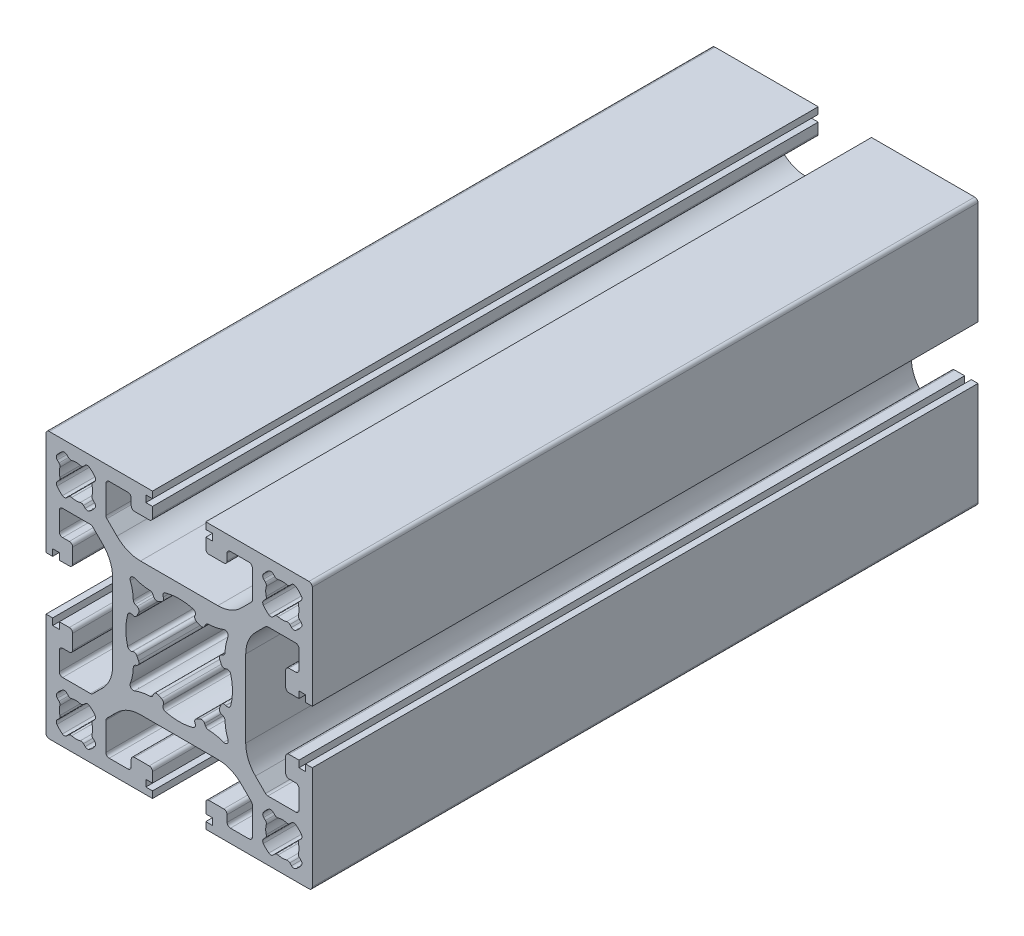
SolidWorks part; units mm, degrees
ref_plane "Front Plane" through (0, 0, 0) normal (0, 0, 1) x (1, 0, 0)
ref_plane "Top Plane" through (0, 0, 0) normal (0, 1, 0) x (1, 0, 0)
ref_plane "Right Plane" through (0, 0, 0) normal (1, 0, 0) x (0, 0, -1)
sketch "Sketch1" plane through (0, 0, 0) normal (0, 0, 1) x (1, 0, 0)
  line L0 (0, -10) -> (0, 10) construction
  line L1 (10, 0) -> (-10, 0) construction
  line L2 (11, 17.5) -> (11, 13.3284)
  line L3 (4, 20) -> (4, 19)
  line L4 (-10.8536, 12.9749) -> (-9.3431, 11.4645)
  line L5 (-12.9749, 10.8536) -> (-11.4645, 9.3431)
  line L6 (19.5, 20) -> (4, 20)
  line L7 (20, 4.5) -> (20, 19.5)
  line L8 (-3.9555, 6.5896) -> (-3.8287, 6.3177)
  line L9 (-2.3966, 7.0325) -> (-2.3786, 6.9939)
  line L10 (-6.7, 16) -> (-4.5, 16)
  line L11 (16.5, 4) -> (18, 4)
  line L12 (16, 6.7) -> (16, 4.5)
  line L13 (13.3284, 11) -> (16, 11)
  line L14 (10, -5.8076) -> (10, 5.8076)
  line L15 (-7.043, 2.3972) -> (-6.995, 2.3748)
  line L16 (-6.599, 3.9553) -> (-6.3199, 3.8254)
  line L17 (-14.1155, 18.2988) -> (-14.37, 18.0442)
  line L18 (18, 4) -> (18, 5)
  line L19 (-12.7012, 16.8845) -> (-12.9558, 16.63)
  line L20 (-10.5, 18) -> (-7.7, 18)
  line L21 (-7.2, 17.5) -> (-7.2, 16.5)
  line L22 (-18.2988, 14.1155) -> (-18.0442, 14.37)
  line L23 (-16.8845, 12.7012) -> (-16.63, 12.9558)
  line L24 (-4, 18) -> (-4, 16.5)
  line L25 (-4, 19) -> (-5, 19)
  line L26 (-18.2988, 16.8845) -> (-18.0442, 16.63)
  line L27 (-16.8845, 18.2988) -> (-16.63, 18.0442)
  line L28 (-16.5, 7.2) -> (-17.5, 7.2)
  line L29 (-4, 18) -> (-5, 18)
  line L30 (-12.7012, 14.1155) -> (-12.9558, 14.37)
  line L31 (-14.1155, 12.7012) -> (-14.37, 12.9558)
  line L32 (-5, 19) -> (-5, 18)
  line L33 (19, 5) -> (18, 5)
  line L34 (19, 4) -> (19, 5)
  line L35 (19, 4) -> (19.5, 4)
  line L36 (17.5, 11) -> (16, 11)
  line L37 (-18, 7.7) -> (-18, 10.5)
  line L38 (-17.5, 11) -> (-16, 11)
  line L39 (-19, 4) -> (-19.5, 4)
  line L40 (18, 7.7) -> (18, 10.5)
  line L41 (-19, 4) -> (-19, 5)
  line L42 (-19, 5) -> (-18, 5)
  line L43 (-18, 4) -> (-18, 5)
  line L44 (5, 19) -> (5, 18)
  line L45 (14.1155, 12.7012) -> (14.37, 12.9558)
  line L46 (12.7012, 14.1155) -> (12.9558, 14.37)
  line L47 (4, 18) -> (5, 18)
  line L48 (-10, -5.8076) -> (-10, 5.8076)
  line L49 (16.5, 7.2) -> (17.5, 7.2)
  line L50 (-13.3284, 11) -> (-16, 11)
  line L51 (-16, 6.7) -> (-16, 4.5)
  line L52 (-16.5, 4) -> (-18, 4)
  line L53 (-20, 4.5) -> (-20, 19.5)
  line L54 (-19.5, 20) -> (-4, 20)
  line L55 (-4, 20) -> (-4, 19)
  line L56 (16.8845, 18.2988) -> (16.63, 18.0442)
  line L57 (-11, 17.5) -> (-11, 13.3284)
  line L58 (18.2988, 16.8845) -> (18.0442, 16.63)
  line L59 (-5.8076, 10) -> (5.8076, 10)
  line L60 (4, 19) -> (5, 19)
  line L61 (4, 18) -> (4, 16.5)
  line L62 (16.8845, 12.7012) -> (16.63, 12.9558)
  line L63 (18.2988, 14.1155) -> (18.0442, 14.37)
  line L64 (7.2, 17.5) -> (7.2, 16.5)
  line L65 (10.5, 18) -> (7.7, 18)
  line L66 (12.7012, 16.8845) -> (12.9558, 16.63)
  line L67 (14.1155, 18.2988) -> (14.37, 18.0442)
  line L68 (6.599, 3.9553) -> (6.3199, 3.8254)
  line L69 (7.043, 2.3972) -> (6.995, 2.3748)
  line L70 (6.7, 16) -> (4.5, 16)
  line L71 (2.3966, 7.0325) -> (2.3786, 6.9939)
  line L72 (3.9555, 6.5896) -> (3.8287, 6.3177)
  line L73 (12.9749, 10.8536) -> (11.4645, 9.3431)
  line L74 (10.8536, 12.9749) -> (9.3431, 11.4645)
  line L75 (10.8536, -12.9749) -> (9.3431, -11.4645)
  line L76 (12.9749, -10.8536) -> (11.4645, -9.3431)
  line L77 (3.9555, -6.5896) -> (3.8287, -6.3177)
  line L78 (2.3966, -7.0325) -> (2.3786, -6.9939)
  line L79 (6.7, -16) -> (4.5, -16)
  line L80 (7.043, -2.3972) -> (6.995, -2.3748)
  line L81 (6.599, -3.9553) -> (6.3199, -3.8254)
  line L82 (14.1155, -18.2988) -> (14.37, -18.0442)
  line L83 (12.7012, -16.8845) -> (12.9558, -16.63)
  line L84 (10.5, -18) -> (7.7, -18)
  line L85 (7.2, -17.5) -> (7.2, -16.5)
  line L86 (18.2988, -14.1155) -> (18.0442, -14.37)
  line L87 (16.8845, -12.7012) -> (16.63, -12.9558)
  line L88 (4, -18) -> (4, -16.5)
  line L89 (4, -19) -> (5, -19)
  line L90 (-5.8076, -10) -> (5.8076, -10)
  line L91 (18.2988, -16.8845) -> (18.0442, -16.63)
  line L92 (-11, -17.5) -> (-11, -13.3284)
  line L93 (16.8845, -18.2988) -> (16.63, -18.0442)
  line L94 (-4, -20) -> (-4, -19)
  line L95 (-19.5, -20) -> (-4, -20)
  line L96 (-20, -4.5) -> (-20, -19.5)
  line L97 (-16.5, -4) -> (-18, -4)
  line L98 (-16, -6.7) -> (-16, -4.5)
  line L99 (-13.3284, -11) -> (-16, -11)
  line L100 (16.5, -7.2) -> (17.5, -7.2)
  line L101 (4, -18) -> (5, -18)
  line L102 (12.7012, -14.1155) -> (12.9558, -14.37)
  line L103 (14.1155, -12.7012) -> (14.37, -12.9558)
  line L104 (5, -19) -> (5, -18)
  line L105 (-18, -4) -> (-18, -5)
  line L106 (-19, -5) -> (-18, -5)
  line L107 (-19, -4) -> (-19, -5)
  line L108 (18, -7.7) -> (18, -10.5)
  line L109 (-19, -4) -> (-19.5, -4)
  line L110 (-17.5, -11) -> (-16, -11)
  line L111 (-18, -7.7) -> (-18, -10.5)
  line L112 (17.5, -11) -> (16, -11)
  line L113 (19, -4) -> (19.5, -4)
  line L114 (19, -4) -> (19, -5)
  line L115 (19, -5) -> (18, -5)
  line L116 (-5, -19) -> (-5, -18)
  line L117 (-14.1155, -12.7012) -> (-14.37, -12.9558)
  line L118 (-12.7012, -14.1155) -> (-12.9558, -14.37)
  line L119 (-4, -18) -> (-5, -18)
  line L120 (-16.5, -7.2) -> (-17.5, -7.2)
  line L121 (-16.8845, -18.2988) -> (-16.63, -18.0442)
  line L122 (-18.2988, -16.8845) -> (-18.0442, -16.63)
  line L123 (-4, -19) -> (-5, -19)
  line L124 (-4, -18) -> (-4, -16.5)
  line L125 (-16.8845, -12.7012) -> (-16.63, -12.9558)
  line L126 (-18.2988, -14.1155) -> (-18.0442, -14.37)
  line L127 (-7.2, -17.5) -> (-7.2, -16.5)
  line L128 (-10.5, -18) -> (-7.7, -18)
  line L129 (-12.7012, -16.8845) -> (-12.9558, -16.63)
  line L130 (18, -4) -> (18, -5)
  line L131 (-14.1155, -18.2988) -> (-14.37, -18.0442)
  line L132 (-6.599, -3.9553) -> (-6.3199, -3.8254)
  line L133 (-7.043, -2.3972) -> (-6.995, -2.3748)
  line L134 (13.3284, -11) -> (16, -11)
  line L135 (16, -6.7) -> (16, -4.5)
  line L136 (16.5, -4) -> (18, -4)
  line L137 (-6.7, -16) -> (-4.5, -16)
  line L138 (-2.3966, -7.0325) -> (-2.3786, -6.9939)
  line L139 (-3.9555, -6.5896) -> (-3.8287, -6.3177)
  line L140 (20, -4.5) -> (20, -19.5)
  line L141 (19.5, -20) -> (4, -20)
  line L142 (-12.9749, -10.8536) -> (-11.4645, -9.3431)
  line L143 (-10.8536, -12.9749) -> (-9.3431, -11.4645)
  line L144 (4, -20) -> (4, -19)
  line L145 (11, -17.5) -> (11, -13.3284)
  line L146 (-20, 4.5) -> (-20, 4)
  line L147 (-20, 4) -> (-19.5, 4)
  line L148 (-20, -4.5) -> (-20, -4)
  line L149 (-20, -4) -> (-19.5, -4)
  line L150 (19.5, 4) -> (20, 4)
  line L151 (20, 4) -> (20, 4.5)
  line L152 (19.5, -4) -> (20, -4)
  line L153 (20, -4) -> (20, -4.5)
  arc A0 (2.073, 7.7267) -> (-2.073, 7.7267) centre (0, 0) ccw
  arc A1 (-6.0865, 3.1427) -> (-6.3226, 2.6358) centre (0, 0) ccw
  arc A2 (-6.6942, 7.3368) -> (-4.3944, 6.8781) centre (-4.1945, 13.8752) ccw
  arc A3 (-2.073, 7.7267) -> (-2.3966, 7.0325) centre (-1.9435, 7.2438) ccw
  arc A4 (-7.7369, 2.0733) -> (-7.7369, -2.0733) centre (0, 0) ccw
  arc A5 (-6.8879, 4.3954) -> (-7.3403, 6.6924) centre (-13.8854, 4.2103) ccw
  arc A6 (-17.9148, 16.147) -> (-17.9148, 14.853) centre (-15.5, 15.5) ccw
  arc A7 (-2.3786, 6.9939) -> (-2.6391, 6.3212) centre (-2.8318, 6.7826) cw
  arc A8 (-3.8287, 6.3177) -> (-3.1459, 6.0849) centre (-3.3755, 6.529) ccw
  arc A9 (-2.6391, 6.3212) -> (-3.1459, 6.0849) centre (0, 0) ccw
  arc A10 (-3.9555, 6.5896) -> (-4.3944, 6.8781) centre (-4.4086, 6.3783) ccw
  arc A11 (-6.6942, 7.3368) -> (-7.3403, 6.6924) centre (-6.8728, 6.8697) ccw
  arc A12 (-6.8879, 4.3954) -> (-6.599, 3.9553) centre (-6.3881, 4.4086) ccw
  arc A13 (-6.3199, 3.8254) -> (-6.0865, 3.1427) centre (-6.5308, 3.3721) cw
  arc A14 (-6.995, 2.3748) -> (-6.3226, 2.6358) centre (-6.7841, 2.8282) ccw
  arc A15 (-7.043, 2.3972) -> (-7.7369, 2.0733) centre (-7.254, 1.9438) ccw
  arc A16 (-17.5278, 18.3527) -> (-18.3527, 17.5278) centre (-15.5, 15.5) ccw
  arc A17 (-14.853, 17.9148) -> (-16.147, 17.9148) centre (-15.5, 15.5) ccw
  arc A18 (-13.0852, 14.853) -> (-13.0852, 16.147) centre (-15.5, 15.5) ccw
  arc A19 (-16.147, 13.0852) -> (-14.853, 13.0852) centre (-15.5, 15.5) ccw
  arc A20 (-18.3527, 13.4722) -> (-17.5278, 12.6473) centre (-15.5, 15.5) ccw
  arc A21 (-13.4722, 12.6473) -> (-12.6473, 13.4722) centre (-15.5, 15.5) ccw
  arc A22 (-12.6473, 17.5278) -> (-13.4722, 18.3527) centre (-15.5, 15.5) ccw
  arc A23 (-4, 16.5) -> (-4.5, 16) centre (-4.5, 16.5) cw
  arc A24 (14.37, 18.0442) -> (14.853, 17.9148) centre (14.7235, 18.3978) ccw
  arc A25 (14.1155, 18.2988) -> (13.4722, 18.3527) centre (13.7619, 17.9452) ccw
  arc A26 (-7.2, 16.5) -> (-6.7, 16) centre (-6.7, 16.5) ccw
  arc A27 (-7.7, 18) -> (-7.2, 17.5) centre (-7.7, 17.5) cw
  arc A28 (-10.5, 18) -> (-11, 17.5) centre (-10.5, 17.5) ccw
  arc A29 (-9.3431, 11.4645) -> (-5.8076, 10) centre (-5.8076, 15) ccw
  arc A30 (-10, 5.8076) -> (-11.4645, 9.3431) centre (-15, 5.8076) ccw
  arc A31 (-10.8536, 12.9749) -> (-11, 13.3284) centre (-10.5, 13.3284) cw
  arc A32 (-12.9749, 10.8536) -> (-13.3284, 11) centre (-13.3284, 10.5) ccw
  arc A33 (-18, 10.5) -> (-17.5, 11) centre (-17.5, 10.5) cw
  arc A34 (-17.5, 7.2) -> (-18, 7.7) centre (-17.5, 7.7) cw
  arc A35 (-16.5, 7.2) -> (-16, 6.7) centre (-16.5, 6.7) cw
  arc A36 (-16, 4.5) -> (-16.5, 4) centre (-16.5, 4.5) cw
  arc A38 (-20, 19.5) -> (-19.5, 20) centre (-19.5, 19.5) cw
  arc A39 (-16.63, 18.0442) -> (-16.147, 17.9148) centre (-16.2765, 18.3978) ccw
  arc A40 (-17.5278, 18.3527) -> (-16.8845, 18.2988) centre (-17.2381, 17.9452) cw
  arc A41 (-18.2988, 16.8845) -> (-18.3527, 17.5278) centre (-17.9452, 17.2381) cw
  arc A42 (-18.0442, 16.63) -> (-17.9148, 16.147) centre (-18.3978, 16.2765) cw
  arc A43 (-18.0442, 14.37) -> (-17.9148, 14.853) centre (-18.3978, 14.7235) ccw
  arc A44 (-18.2988, 14.1155) -> (-18.3527, 13.4722) centre (-17.9452, 13.7619) ccw
  arc A45 (-17.5278, 12.6473) -> (-16.8845, 12.7012) centre (-17.2381, 13.0548) ccw
  arc A46 (-16.63, 12.9558) -> (-16.147, 13.0852) centre (-16.2765, 12.6022) cw
  arc A47 (-14.37, 12.9558) -> (-14.853, 13.0852) centre (-14.7235, 12.6022) ccw
  arc A48 (-13.4722, 12.6473) -> (-14.1155, 12.7012) centre (-13.7619, 13.0548) cw
  arc A49 (-12.7012, 14.1155) -> (-12.6473, 13.4722) centre (-13.0548, 13.7619) cw
  arc A50 (-12.9558, 14.37) -> (-13.0852, 14.853) centre (-12.6022, 14.7235) cw
  arc A51 (-12.9558, 16.63) -> (-13.0852, 16.147) centre (-12.6022, 16.2765) ccw
  arc A52 (-12.6473, 17.5278) -> (-12.7012, 16.8845) centre (-13.0548, 17.2381) cw
  arc A53 (-14.1155, 18.2988) -> (-13.4722, 18.3527) centre (-13.7619, 17.9452) cw
  arc A54 (-14.37, 18.0442) -> (-14.853, 17.9148) centre (-14.7235, 18.3978) cw
  arc A55 (12.6473, 17.5278) -> (12.7012, 16.8845) centre (13.0548, 17.2381) ccw
  arc A56 (12.9558, 16.63) -> (13.0852, 16.147) centre (12.6022, 16.2765) cw
  arc A57 (12.9558, 14.37) -> (13.0852, 14.853) centre (12.6022, 14.7235) ccw
  arc A58 (12.7012, 14.1155) -> (12.6473, 13.4722) centre (13.0548, 13.7619) ccw
  arc A59 (13.4722, 12.6473) -> (14.1155, 12.7012) centre (13.7619, 13.0548) ccw
  arc A60 (14.37, 12.9558) -> (14.853, 13.0852) centre (14.7235, 12.6022) cw
  arc A61 (16.63, 12.9558) -> (16.147, 13.0852) centre (16.2765, 12.6022) ccw
  arc A62 (17.5278, 12.6473) -> (16.8845, 12.7012) centre (17.2381, 13.0548) cw
  arc A63 (18.2988, 14.1155) -> (18.3527, 13.4722) centre (17.9452, 13.7619) cw
  arc A64 (18.0442, 14.37) -> (17.9148, 14.853) centre (18.3978, 14.7235) cw
  arc A65 (18.0442, 16.63) -> (17.9148, 16.147) centre (18.3978, 16.2765) ccw
  arc A66 (18.2988, 16.8845) -> (18.3527, 17.5278) centre (17.9452, 17.2381) ccw
  arc A67 (17.5278, 18.3527) -> (16.8845, 18.2988) centre (17.2381, 17.9452) ccw
  arc A68 (16.63, 18.0442) -> (16.147, 17.9148) centre (16.2765, 18.3978) cw
  arc A69 (20, 19.5) -> (19.5, 20) centre (19.5, 19.5) ccw
  arc A71 (16, 4.5) -> (16.5, 4) centre (16.5, 4.5) ccw
  arc A72 (16.5, 7.2) -> (16, 6.7) centre (16.5, 6.7) ccw
  arc A73 (17.5, 7.2) -> (18, 7.7) centre (17.5, 7.7) ccw
  arc A74 (18, 10.5) -> (17.5, 11) centre (17.5, 10.5) ccw
  arc A75 (12.9749, 10.8536) -> (13.3284, 11) centre (13.3284, 10.5) cw
  arc A76 (10.8536, 12.9749) -> (11, 13.3284) centre (10.5, 13.3284) ccw
  arc A77 (10, 5.8076) -> (11.4645, 9.3431) centre (15, 5.8076) cw
  arc A78 (9.3431, 11.4645) -> (5.8076, 10) centre (5.8076, 15) cw
  arc A79 (10.5, 18) -> (11, 17.5) centre (10.5, 17.5) cw
  arc A80 (7.7, 18) -> (7.2, 17.5) centre (7.7, 17.5) ccw
  arc A81 (7.2, 16.5) -> (6.7, 16) centre (6.7, 16.5) cw
  arc A82 (4, 16.5) -> (4.5, 16) centre (4.5, 16.5) ccw
  arc A83 (12.6473, 17.5278) -> (13.4722, 18.3527) centre (15.5, 15.5) cw
  arc A84 (13.4722, 12.6473) -> (12.6473, 13.4722) centre (15.5, 15.5) cw
  arc A85 (18.3527, 13.4722) -> (17.5278, 12.6473) centre (15.5, 15.5) cw
  arc A86 (16.147, 13.0852) -> (14.853, 13.0852) centre (15.5, 15.5) cw
  arc A87 (13.0852, 14.853) -> (13.0852, 16.147) centre (15.5, 15.5) cw
  arc A88 (14.853, 17.9148) -> (16.147, 17.9148) centre (15.5, 15.5) cw
  arc A89 (17.5278, 18.3527) -> (18.3527, 17.5278) centre (15.5, 15.5) cw
  arc A90 (7.043, 2.3972) -> (7.7369, 2.0733) centre (7.254, 1.9438) cw
  arc A91 (6.995, 2.3748) -> (6.3226, 2.6358) centre (6.7841, 2.8282) cw
  arc A92 (6.3199, 3.8254) -> (6.0865, 3.1427) centre (6.5308, 3.3721) ccw
  arc A93 (6.8879, 4.3954) -> (6.599, 3.9553) centre (6.3881, 4.4086) cw
  arc A94 (6.6942, 7.3368) -> (7.3403, 6.6924) centre (6.8728, 6.8697) cw
  arc A95 (3.9555, 6.5896) -> (4.3944, 6.8781) centre (4.4086, 6.3783) cw
  arc A96 (2.6391, 6.3212) -> (3.1459, 6.0849) centre (0, 0) cw
  arc A97 (3.8287, 6.3177) -> (3.1459, 6.0849) centre (3.3755, 6.529) cw
  arc A98 (2.3786, 6.9939) -> (2.6391, 6.3212) centre (2.8318, 6.7826) ccw
  arc A99 (17.9148, 16.147) -> (17.9148, 14.853) centre (15.5, 15.5) cw
  arc A100 (6.8879, 4.3954) -> (7.3403, 6.6924) centre (13.8854, 4.2103) cw
  arc A101 (7.7369, 2.0733) -> (7.7369, -2.0733) centre (0, 0) cw
  arc A102 (2.073, 7.7267) -> (2.3966, 7.0325) centre (1.9435, 7.2438) cw
  arc A103 (6.6942, 7.3368) -> (4.3944, 6.8781) centre (4.1945, 13.8752) cw
  arc A104 (6.0865, 3.1427) -> (6.3226, 2.6358) centre (0, 0) cw
  arc A105 (6.0865, -3.1427) -> (6.3226, -2.6358) centre (0, 0) ccw
  arc A106 (6.6942, -7.3368) -> (4.3944, -6.8781) centre (4.1945, -13.8752) ccw
  arc A107 (2.073, -7.7267) -> (2.3966, -7.0325) centre (1.9435, -7.2438) ccw
  arc A108 (6.8879, -4.3954) -> (7.3403, -6.6924) centre (13.8854, -4.2103) ccw
  arc A109 (17.9148, -16.147) -> (17.9148, -14.853) centre (15.5, -15.5) ccw
  arc A110 (2.3786, -6.9939) -> (2.6391, -6.3212) centre (2.8318, -6.7826) cw
  arc A111 (3.8287, -6.3177) -> (3.1459, -6.0849) centre (3.3755, -6.529) ccw
  arc A112 (2.6391, -6.3212) -> (3.1459, -6.0849) centre (0, 0) ccw
  arc A113 (3.9555, -6.5896) -> (4.3944, -6.8781) centre (4.4086, -6.3783) ccw
  arc A114 (6.6942, -7.3368) -> (7.3403, -6.6924) centre (6.8728, -6.8697) ccw
  arc A115 (6.8879, -4.3954) -> (6.599, -3.9553) centre (6.3881, -4.4086) ccw
  arc A116 (6.3199, -3.8254) -> (6.0865, -3.1427) centre (6.5308, -3.3721) cw
  arc A117 (6.995, -2.3748) -> (6.3226, -2.6358) centre (6.7841, -2.8282) ccw
  arc A118 (7.043, -2.3972) -> (7.7369, -2.0733) centre (7.254, -1.9438) ccw
  arc A119 (17.5278, -18.3527) -> (18.3527, -17.5278) centre (15.5, -15.5) ccw
  arc A120 (14.853, -17.9148) -> (16.147, -17.9148) centre (15.5, -15.5) ccw
  arc A121 (13.0852, -14.853) -> (13.0852, -16.147) centre (15.5, -15.5) ccw
  arc A122 (16.147, -13.0852) -> (14.853, -13.0852) centre (15.5, -15.5) ccw
  arc A123 (18.3527, -13.4722) -> (17.5278, -12.6473) centre (15.5, -15.5) ccw
  arc A124 (13.4722, -12.6473) -> (12.6473, -13.4722) centre (15.5, -15.5) ccw
  arc A125 (12.6473, -17.5278) -> (13.4722, -18.3527) centre (15.5, -15.5) ccw
  arc A126 (4, -16.5) -> (4.5, -16) centre (4.5, -16.5) cw
  arc A127 (7.2, -16.5) -> (6.7, -16) centre (6.7, -16.5) ccw
  arc A128 (7.7, -18) -> (7.2, -17.5) centre (7.7, -17.5) cw
  arc A129 (10.5, -18) -> (11, -17.5) centre (10.5, -17.5) ccw
  arc A130 (9.3431, -11.4645) -> (5.8076, -10) centre (5.8076, -15) ccw
  arc A131 (10, -5.8076) -> (11.4645, -9.3431) centre (15, -5.8076) ccw
  arc A132 (10.8536, -12.9749) -> (11, -13.3284) centre (10.5, -13.3284) cw
  arc A133 (12.9749, -10.8536) -> (13.3284, -11) centre (13.3284, -10.5) ccw
  arc A134 (18, -10.5) -> (17.5, -11) centre (17.5, -10.5) cw
  arc A135 (17.5, -7.2) -> (18, -7.7) centre (17.5, -7.7) cw
  arc A136 (16.5, -7.2) -> (16, -6.7) centre (16.5, -6.7) cw
  arc A137 (16, -4.5) -> (16.5, -4) centre (16.5, -4.5) cw
  arc A139 (20, -19.5) -> (19.5, -20) centre (19.5, -19.5) cw
  arc A140 (16.63, -18.0442) -> (16.147, -17.9148) centre (16.2765, -18.3978) ccw
  arc A141 (17.5278, -18.3527) -> (16.8845, -18.2988) centre (17.2381, -17.9452) cw
  arc A142 (18.2988, -16.8845) -> (18.3527, -17.5278) centre (17.9452, -17.2381) cw
  arc A143 (18.0442, -16.63) -> (17.9148, -16.147) centre (18.3978, -16.2765) cw
  arc A144 (18.0442, -14.37) -> (17.9148, -14.853) centre (18.3978, -14.7235) ccw
  arc A145 (18.2988, -14.1155) -> (18.3527, -13.4722) centre (17.9452, -13.7619) ccw
  arc A146 (17.5278, -12.6473) -> (16.8845, -12.7012) centre (17.2381, -13.0548) ccw
  arc A147 (16.63, -12.9558) -> (16.147, -13.0852) centre (16.2765, -12.6022) cw
  arc A148 (14.37, -12.9558) -> (14.853, -13.0852) centre (14.7235, -12.6022) ccw
  arc A149 (13.4722, -12.6473) -> (14.1155, -12.7012) centre (13.7619, -13.0548) cw
  arc A150 (12.7012, -14.1155) -> (12.6473, -13.4722) centre (13.0548, -13.7619) cw
  arc A151 (12.9558, -14.37) -> (13.0852, -14.853) centre (12.6022, -14.7235) cw
  arc A152 (12.9558, -16.63) -> (13.0852, -16.147) centre (12.6022, -16.2765) ccw
  arc A153 (12.6473, -17.5278) -> (12.7012, -16.8845) centre (13.0548, -17.2381) cw
  arc A154 (-14.37, -18.0442) -> (-14.853, -17.9148) centre (-14.7235, -18.3978) ccw
  arc A155 (-14.1155, -18.2988) -> (-13.4722, -18.3527) centre (-13.7619, -17.9452) ccw
  arc A156 (-12.6473, -17.5278) -> (-12.7012, -16.8845) centre (-13.0548, -17.2381) ccw
  arc A157 (-12.9558, -16.63) -> (-13.0852, -16.147) centre (-12.6022, -16.2765) cw
  arc A158 (-12.9558, -14.37) -> (-13.0852, -14.853) centre (-12.6022, -14.7235) ccw
  arc A159 (-12.7012, -14.1155) -> (-12.6473, -13.4722) centre (-13.0548, -13.7619) ccw
  arc A160 (-13.4722, -12.6473) -> (-14.1155, -12.7012) centre (-13.7619, -13.0548) ccw
  arc A161 (-14.37, -12.9558) -> (-14.853, -13.0852) centre (-14.7235, -12.6022) cw
  arc A162 (-16.63, -12.9558) -> (-16.147, -13.0852) centre (-16.2765, -12.6022) ccw
  arc A163 (-17.5278, -12.6473) -> (-16.8845, -12.7012) centre (-17.2381, -13.0548) cw
  arc A164 (-18.2988, -14.1155) -> (-18.3527, -13.4722) centre (-17.9452, -13.7619) cw
  arc A165 (-18.0442, -14.37) -> (-17.9148, -14.853) centre (-18.3978, -14.7235) cw
  arc A166 (-18.0442, -16.63) -> (-17.9148, -16.147) centre (-18.3978, -16.2765) ccw
  arc A167 (-18.2988, -16.8845) -> (-18.3527, -17.5278) centre (-17.9452, -17.2381) ccw
  arc A168 (-17.5278, -18.3527) -> (-16.8845, -18.2988) centre (-17.2381, -17.9452) ccw
  arc A169 (-16.63, -18.0442) -> (-16.147, -17.9148) centre (-16.2765, -18.3978) cw
  arc A170 (-20, -19.5) -> (-19.5, -20) centre (-19.5, -19.5) ccw
  arc A172 (-16, -4.5) -> (-16.5, -4) centre (-16.5, -4.5) ccw
  arc A173 (-16.5, -7.2) -> (-16, -6.7) centre (-16.5, -6.7) ccw
  arc A174 (-17.5, -7.2) -> (-18, -7.7) centre (-17.5, -7.7) ccw
  arc A175 (-18, -10.5) -> (-17.5, -11) centre (-17.5, -10.5) ccw
  arc A176 (-12.9749, -10.8536) -> (-13.3284, -11) centre (-13.3284, -10.5) cw
  arc A177 (-10.8536, -12.9749) -> (-11, -13.3284) centre (-10.5, -13.3284) ccw
  arc A178 (-10, -5.8076) -> (-11.4645, -9.3431) centre (-15, -5.8076) cw
  arc A179 (-9.3431, -11.4645) -> (-5.8076, -10) centre (-5.8076, -15) cw
  arc A180 (-10.5, -18) -> (-11, -17.5) centre (-10.5, -17.5) cw
  arc A181 (-7.7, -18) -> (-7.2, -17.5) centre (-7.7, -17.5) ccw
  arc A182 (-7.2, -16.5) -> (-6.7, -16) centre (-6.7, -16.5) cw
  arc A183 (14.1155, -18.2988) -> (13.4722, -18.3527) centre (13.7619, -17.9452) cw
  arc A184 (14.37, -18.0442) -> (14.853, -17.9148) centre (14.7235, -18.3978) cw
  arc A185 (-4, -16.5) -> (-4.5, -16) centre (-4.5, -16.5) ccw
  arc A186 (-12.6473, -17.5278) -> (-13.4722, -18.3527) centre (-15.5, -15.5) cw
  arc A187 (-13.4722, -12.6473) -> (-12.6473, -13.4722) centre (-15.5, -15.5) cw
  arc A188 (-18.3527, -13.4722) -> (-17.5278, -12.6473) centre (-15.5, -15.5) cw
  arc A189 (-16.147, -13.0852) -> (-14.853, -13.0852) centre (-15.5, -15.5) cw
  arc A190 (-13.0852, -14.853) -> (-13.0852, -16.147) centre (-15.5, -15.5) cw
  arc A191 (-14.853, -17.9148) -> (-16.147, -17.9148) centre (-15.5, -15.5) cw
  arc A192 (-17.5278, -18.3527) -> (-18.3527, -17.5278) centre (-15.5, -15.5) cw
  arc A193 (-7.043, -2.3972) -> (-7.7369, -2.0733) centre (-7.254, -1.9438) cw
  arc A194 (-6.995, -2.3748) -> (-6.3226, -2.6358) centre (-6.7841, -2.8282) cw
  arc A195 (-6.3199, -3.8254) -> (-6.0865, -3.1427) centre (-6.5308, -3.3721) ccw
  arc A196 (-6.8879, -4.3954) -> (-6.599, -3.9553) centre (-6.3881, -4.4086) cw
  arc A197 (-6.6942, -7.3368) -> (-7.3403, -6.6924) centre (-6.8728, -6.8697) cw
  arc A198 (-3.9555, -6.5896) -> (-4.3944, -6.8781) centre (-4.4086, -6.3783) cw
  arc A199 (-2.6391, -6.3212) -> (-3.1459, -6.0849) centre (0, 0) cw
  arc A200 (-3.8287, -6.3177) -> (-3.1459, -6.0849) centre (-3.3755, -6.529) cw
  arc A201 (-2.3786, -6.9939) -> (-2.6391, -6.3212) centre (-2.8318, -6.7826) ccw
  arc A202 (-17.9148, -16.147) -> (-17.9148, -14.853) centre (-15.5, -15.5) cw
  arc A203 (-6.8879, -4.3954) -> (-7.3403, -6.6924) centre (-13.8854, -4.2103) cw
  arc A204 (-2.073, -7.7267) -> (-2.3966, -7.0325) centre (-1.9435, -7.2438) cw
  arc A205 (-6.6942, -7.3368) -> (-4.3944, -6.8781) centre (-4.1945, -13.8752) cw
  arc A206 (-6.0865, -3.1427) -> (-6.3226, -2.6358) centre (0, 0) cw
  arc A207 (2.073, -7.7267) -> (-2.073, -7.7267) centre (0, 0) cw
  point P46 (-4.089, 6.876)
  point P49 (-8, 8)
  point P54 (-5.8294, 3.5972)
  point P102 (-4, 19)
  point P137 (-18.5788, 13.8354)
  point P140 (-17.1646, 12.4212)
  point P143 (-16.4131, 13.1727)
  point P148 (-13.8354, 12.4212)
  point P151 (-12.4212, 13.8354)
  point P158 (-12.4212, 17.1646)
  point P161 (-13.8354, 18.5788)
  point P277 (13.8354, 18.5788)
  point P278 (12.4212, 17.1646)
  point P279 (12.4212, 13.8354)
  point P280 (13.8354, 12.4212)
  point P281 (16.4131, 13.1727)
  point P282 (17.1646, 12.4212)
  point P283 (18.5788, 13.8354)
  point P284 (5.8294, 3.5972)
  point P285 (8, 8)
  point P286 (4.089, 6.876)
  point P546 (4.089, -6.876)
  point P547 (8, -8)
  point P548 (5.8294, -3.5972)
  point P549 (18.5788, -13.8354)
  point P550 (17.1646, -12.4212)
  point P551 (16.4131, -13.1727)
  point P552 (13.8354, -12.4212)
  point P553 (12.4212, -13.8354)
  point P554 (12.4212, -17.1646)
  point P555 (13.8354, -18.5788)
  point P556 (-13.8354, -18.5788)
  point P557 (-12.4212, -17.1646)
  point P558 (-12.4212, -13.8354)
  point P559 (-13.8354, -12.4212)
  point P560 (-16.4131, -13.1727)
  point P561 (-17.1646, -12.4212)
  point P562 (-18.5788, -13.8354)
  point P563 (-5.8294, -3.5972)
  point P564 (-8, -8)
  point P565 (-4.089, -6.876)
extrude "Extrude1" add sketch "Sketch1" against normal blind 100
